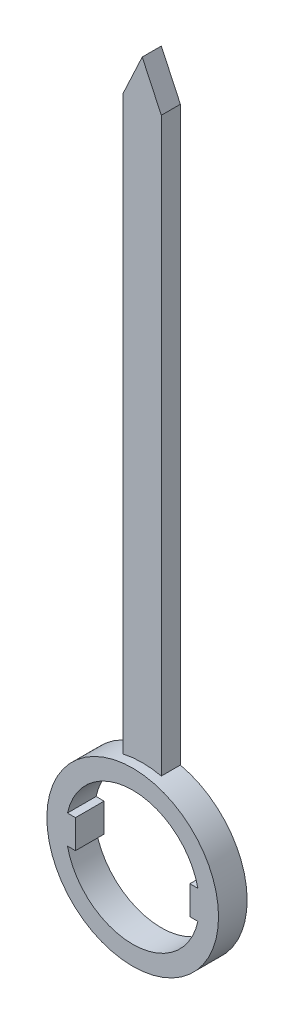
SolidWorks part; units mm, degrees
ref_plane "Front Plane" through (0, 0, 0) normal (0, 0, 1) x (1, 0, 0)
ref_plane "Top Plane" through (0, 0, 0) normal (0, 1, 0) x (1, 0, 0)
ref_plane "Right Plane" through (0, 0, 0) normal (1, 0, 0) x (0, 0, -1)
sketch "Sketch1" plane through (0, 0, 0) normal (0, 0, 1) x (1, 0, 0)
  line L0 (0, 0) -> (2.1795, 0) construction
  line L1 (0, 4.9672) -> (0, 4.5218) construction
  line L2 (-8, -1.5) -> (-6, -1.5)
  line L3 (-8, -1.5) -> (-8, 1.5)
  line L4 (-8, 1.5) -> (-6, 1.5)
  line L5 (-6, -1.5) -> (-6, 1.5)
  line L6 (-8, -1.5) -> (-6, 1.5) construction
  line L7 (-8, 1.5) -> (-6, -1.5) construction
  line L8 (8, 1.5) -> (6, 1.5)
  line L9 (6, -1.5) -> (6, 1.5)
  line L10 (8, -1.5) -> (6, -1.5)
  line L11 (8, -1.5) -> (8, 1.5)
  circle A0 centre (0, 0) radius 7
  circle A1 centre (0, 0) radius 2.5 construction
  circle A2 centre (0, 0) radius 9
  point P5 (-7, 0)
  dimension "D1" = 14
  dimension "D2" = 5
  dimension "D5" = 18
  dimension "D3" = 6
  dimension "D4" = 3
extrude "Boss-Extrude1" add sketch "Sketch1" along normal blind 3 contours A2 A0 L8 L11 L10 L2 L3 L4 | L10 A0 L8 L9 | A0 L10 L11 L8 | A0 L4 L3 L2 | L4 A0 L2 L5
sketch "Sketch2" plane through (0, 0, 0) normal (0, 0, -1) x (-1, 0, 0)
  line L0 (0, 9.6113) -> (0, 8.1441) construction
  line L1 (-2, 8.775) -> (-2, 68.775)
  line L2 (-2, 68.775) -> (0, 73.064)
  line L3 (0, 73.064) -> (2, 68.775)
  line L4 (2, 68.775) -> (2, 8.775)
  circle A0 centre (0, 0) radius 9 construction
  circle A1 centre (0, 0) radius 9
  circle M15 centre (0, 0) radius 9
  dimension "D1" = 2
  dimension "D2" = 2
  dimension "D3" = 60
  dimension "D4" = 205
extrude "Boss-Extrude2" add sketch "Sketch2" against normal blind 2 contours L0 L2 L1 A1 | L3 L0 L4 M15
